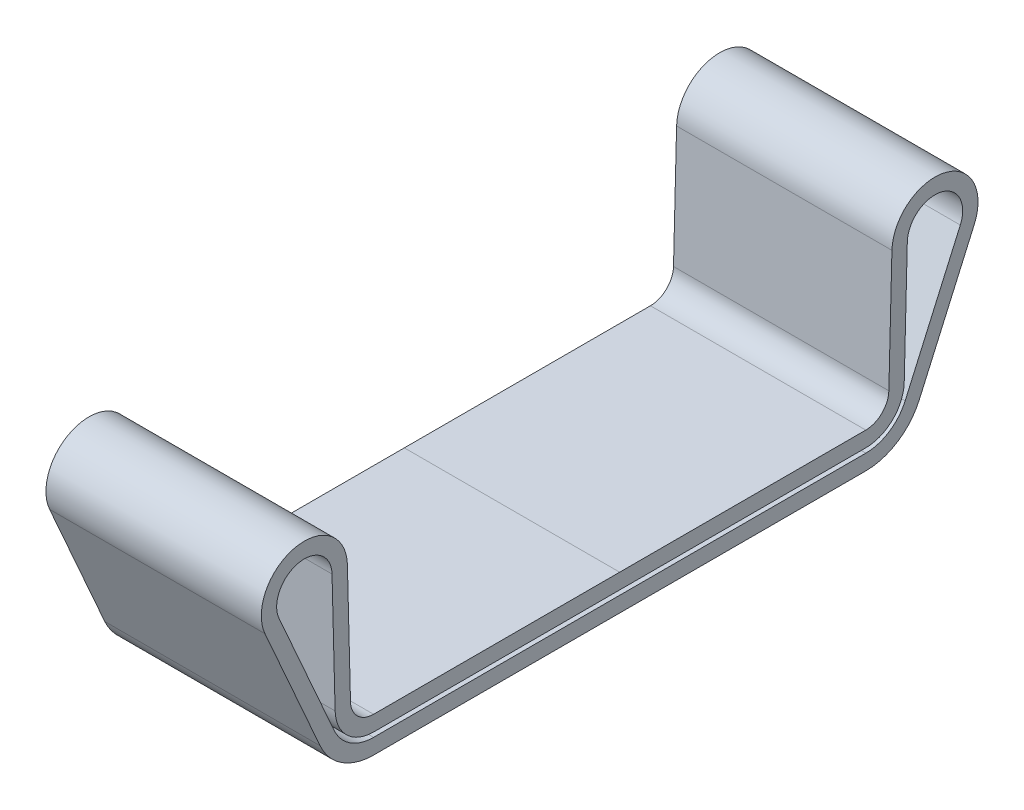
SolidWorks part; units mm, degrees
ref_plane "Front Plane" through (0, 0, 0) normal (0, 0, 1) x (1, 0, 0)
ref_plane "Top Plane" through (0, 0, 0) normal (0, 1, 0) x (1, 0, 0)
ref_plane "Right Plane" through (0, 0, 0) normal (1, 0, 0) x (0, 0, -1)
sketch "Sketch1" plane through (0, 0, 0) normal (1, 0, 0) x (0, 0, -1)
  line L1 (-22.1461, 6.7718) -> (-18.5612, -1.3327)
  line L2 (-18.7006, 7.5463) -> (-18.4997, -0.2643)
  line L3 (0, -2.7) -> (-16.0005, -2.7)
  line L4 (0, -1.7) -> (0, -2.7)
  line L5 (0, -2.7) -> (0, -3) construction
  line L6 (0, -3) -> (0, -4)
  line L7 (0, -3) -> (-16.0005, -3)
  line L9 (14.258, -2.7) -> (-16.0005, -2.7) construction
  line L10 (15.5346, -1.7) -> (-16.0005, -1.7) construction
  line L12 (0, -4) -> (-16.0005, -4)
  line L13 (-19.4757, -1.7372) -> (-23.0607, 6.3673)
  line L15 (-17.7009, 7.572) -> (-17.5, -0.2386)
  line L16 (0, -1.7) -> (-16.0005, -1.7)
  line L17 (17.0515, -4.1758) -> (20.2751, -1.0699) construction
  line L18 (20.2751, -1.0699) -> (20.2729, -4.8168) construction
  line L19 (21.2764, 1.2835) -> (21.2736, -3.5425) construction
  line L20 (16.4955, -3.3229) -> (21.2764, 1.2835) construction
  line L21 (-17.7009, 7.572) -> (-17.8705, 14.1644) construction
  line L22 (-18.7006, 7.5463) -> (-18.8834, 14.6537) construction
  line L23 (-12.1362, 17) -> (18.298, 17.0003) construction
  line L24 (-12.1362, 16) -> (18.298, 16.0003) construction
  arc A0 (-18.7006, 7.5463) -> (-22.1461, 6.7718) centre (-20.5, 7.5) ccw
  arc A2 (-17.7009, 7.572) -> (-23.0607, 6.3673) centre (-20.5, 7.5) ccw
  arc A3 (-17.5, -0.2386) -> (-16.0005, -1.7) centre (-16.0005, -0.2) ccw
  arc A4 (-18.4997, -0.2643) -> (-16.0005, -2.7) centre (-16.0005, -0.2) ccw
  arc A6 (-18.5612, -1.3327) -> (-16.0005, -3) centre (-16.0005, -0.2) ccw
  arc A7 (-16.0005, -4) -> (-19.4757, -1.7372) centre (-16.0005, -0.2) cw
  arc A9 (18.298, 16.0003) -> (21.2736, -3.5425) centre (18.2981, 6.0024) cw construction
  arc A10 (17.0515, -4.1758) -> (14.258, -2.7) centre (16.203, -2.4002) cw construction
  arc A11 (16.4955, -3.3229) -> (15.5346, -1.7) centre (16.203, -2.4002) cw construction
  arc A12 (18.298, 17.0003) -> (20.2729, -4.8168) centre (18.2981, 6.0024) cw construction
  arc A13 (-18.8834, 14.6537) -> (-12.1362, 17) centre (-12.1361, 6.1247) cw construction
  arc A14 (-17.8705, 14.1644) -> (-12.1362, 16) centre (-12.1361, 6.1247) cw construction
  point P0 (0, 0)
  point P6 (0, 0)
  point P27 (-17.4624, -1.7)
  dimension "D3" = 1
  dimension "D1" = 1.8
  dimension "D5" = 1.5
  dimension "D2" = 0.3
  dimension "D4" = 1
  dimension "D6" = 1.7
  dimension "D7" = 20.5
  dimension "D8" = 7.5
  dimension "D9" = 17.5
extrude "Boss-Extrude1" add sketch "Sketch1" along normal mid plane 14
mirror "Mirror1" about plane through (0, 0, 0) normal (0, 0, 1) of "Boss-Extrude1"
